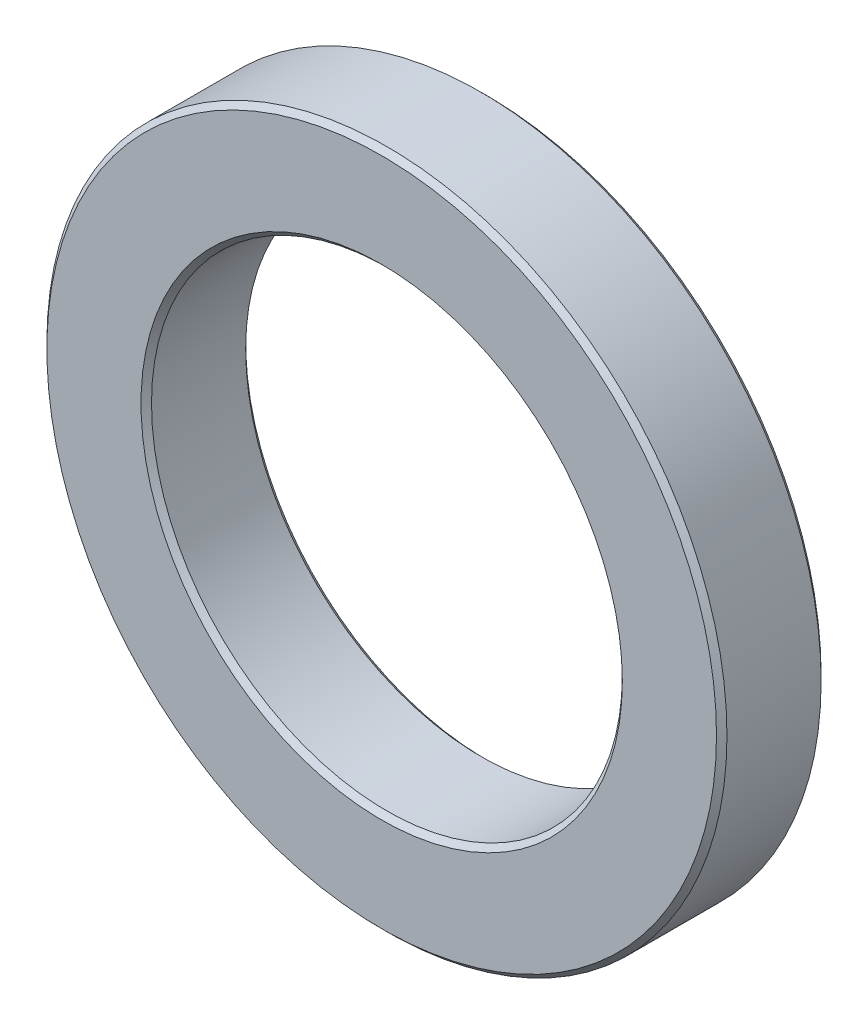
SolidWorks part; units mm, degrees
ref_plane "Front Plane" through (0, 0, 0) normal (0, 0, 1) x (1, 0, 0)
ref_plane "Top Plane" through (0, 0, 0) normal (0, 1, 0) x (1, 0, 0)
ref_plane "Right Plane" through (0, 0, 0) normal (1, 0, 0) x (0, 0, -1)
sketch "Sketch3" plane through (0, 0, 0) normal (0, 0, 1) x (1, 0, 0)
  circle A0 centre (0, 0) radius 32.5
  circle A1 centre (0, 0) radius 22.5
  dimension "D1" = 65
  dimension "D2" = 45
extrude "Boss-Extrude1" add sketch "Sketch3" along normal blind 10
chamfer "Chamfer1" distance 0.5 angle 45 4 edges at (32.5, 0, 0) (22.5, 0, 0) (22.5, 0, 10) (32.5, 0, 10)
